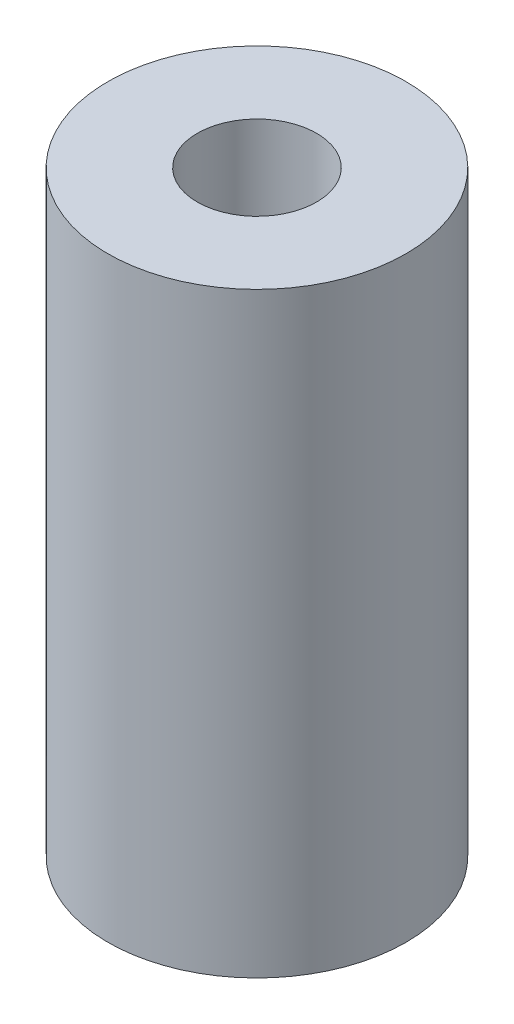
SolidWorks part; units mm, degrees
ref_plane "Front Plane" through (0, 0, 0) normal (0, 0, 1) x (1, 0, 0)
ref_plane "Top Plane" through (0, 0, 0) normal (0, 1, 0) x (1, 0, 0)
ref_plane "Right Plane" through (0, 0, 0) normal (1, 0, 0) x (0, 0, -1)
sketch "Sketch1" plane through (0, 0, 0) normal (0, 1, 0) x (1, 0, 0)
  circle A0 centre (0, 0) radius 1
  dimension "D1" = 2
extrude "Extrude-Thin1" add sketch "Sketch1" along normal blind 10 thin
